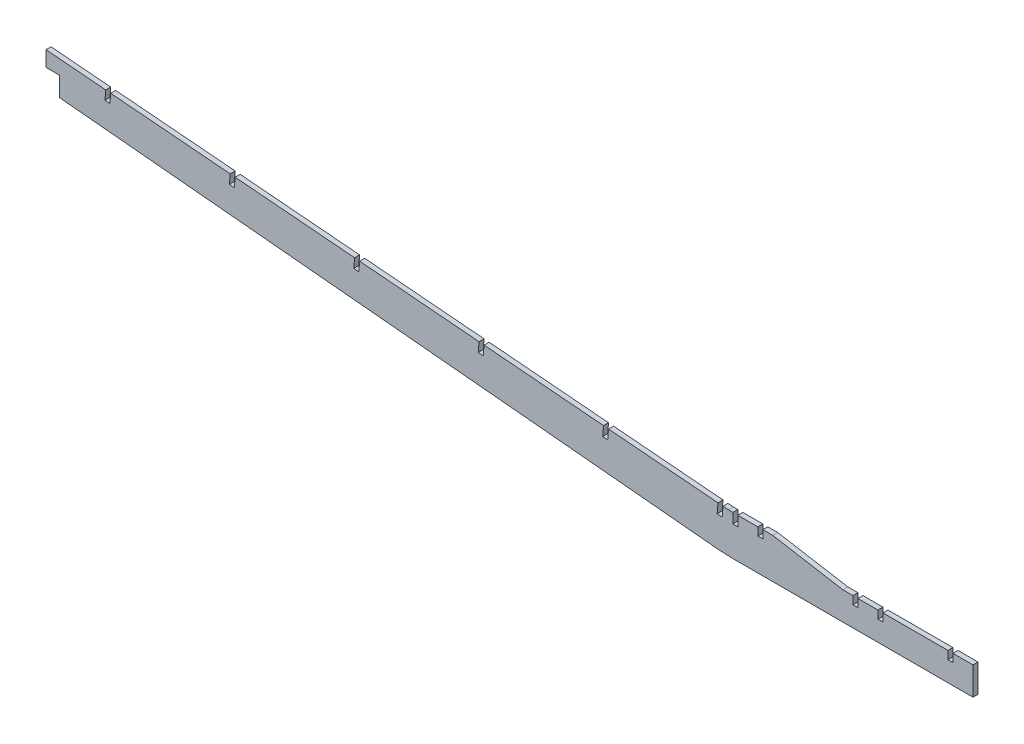
SolidWorks part; units mm, degrees
ref_plane "Front Plane" through (0, 0, 0) normal (0, 0, 1) x (1, 0, 0)
ref_plane "Top Plane" through (0, 0, 0) normal (0, 1, 0) x (1, 0, 0)
ref_plane "Right Plane" through (0, 0, 0) normal (1, 0, 0) x (0, 0, -1)
sketch "Sketch1" plane through (0, 0, 0) normal (0, 0, 1) x (1, 0, 0)
  line L0 (-951.0618, 63.2916) -> (-11.5367, -24.9026)
  line L8 (-8.3728, -25.1683) -> (-6.7788, -6.1851) construction
  line L9 (-6.7788, -6.1851) -> (-9.9426, -5.9194)
  line L10 (-9.9426, -5.9194) -> (-11.5367, -24.9026) construction
  line L11 (-11.5367, -24.9026) -> (-8.3728, -25.1683)
  line L12 (3.175, -25.5459) -> (3.175, -6.4959) construction
  line L13 (3.175, -6.4959) -> (0, -6.4959)
  line L14 (0, -6.4959) -> (0, -25.5459) construction
  line L15 (0, -25.5459) -> (3.175, -25.5459)
  line L17 (-943.9754, 109.7383) -> (-947.3666, 69.3536)
  line L19 (-8.3728, -25.1683) -> (0, -25.5459)
  line L20 (3.175, -25.5459) -> (152.4, -25.5459)
  line L21 (25.4, -0.1459) -> (69.85, -7.7659)
  line L22 (25.4, -0.1459) -> (-2.8123, -0.1459)
  line L23 (-2.8123, -0.1459) -> (-946.5481, 79.1019)
  line L24 (0, -6.4959) -> (0, -0.1459)
  line L25 (3.175, -6.4959) -> (3.175, -0.1459)
  line L26 (-6.7788, -6.1851) -> (-6.2474, 0.1426)
  line L27 (-9.9426, -5.9194) -> (-9.4113, 0.4083)
  line L28 (-9.9426, -5.9194) -> (-946.998, 73.7432)
  line L29 (69.85, -7.7659) -> (152.4, -7.7659)
  line L30 (152.4, -7.7659) -> (152.4, -25.5459)
  line L31 (76.2, -7.7659) -> (76.2, -25.5459)
  line L32 (79.375, -7.7659) -> (79.375, -25.5459)
  line L33 (76.2, -12.8459) -> (79.375, -12.8459)
  line L34 (15.875, -0.1459) -> (15.875, -5.2259)
  line L35 (15.875, -5.2259) -> (19.05, -5.2259)
  line L36 (19.05, -5.2259) -> (19.05, -0.1459)
  line L37 (92.075, -7.7659) -> (92.075, -12.8459)
  line L38 (92.075, -12.8459) -> (95.25, -12.8459)
  line L39 (95.25, -12.8459) -> (95.25, -7.7659)
  line L40 (136.525, -7.7659) -> (136.525, -12.8459)
  line L41 (136.525, -12.8459) -> (139.7, -12.8459)
  line L42 (139.7, -12.8459) -> (139.7, -7.7659)
  line L44 (-951.0618, 63.2916) -> (-950.5305, 69.6193)
  line L45 (-950.5305, 69.6193) -> (-947.3666, 69.3536)
  dimension "D1" = 25.4
  dimension "D2" = 6.35
extrude "Boss-Extrude1" add sketch "Sketch1" along normal blind 3.175
sketch "Sketch2" plane through (0, 0, 3.175) normal (0, 0, 1) x (1, 0, 0)
  line L1 (-73.9963, 64.5177) -> (-80.9723, -18.558)
  line L3 (-77.1601, 64.7834) -> (-84.1362, -18.2923)
  line L5 (-153.17, 68.7234) -> (-159.8855, -11.2491)
  line L7 (-232.3428, 72.9404) -> (-238.7996, -3.951)
  line L9 (-311.5203, 77.1018) -> (-317.7101, 3.3887)
  line L11 (-390.6978, 81.2631) -> (-396.6209, 10.7264)
  line L13 (-469.8812, 85.3537) -> (-475.5272, 18.1169)
  line L15 (-549.0652, 89.4374) -> (-554.4332, 25.5108)
  line L17 (-628.256, 93.4393) -> (-633.334, 32.9679)
  line L19 (-707.4489, 97.4177) -> (-712.2332, 40.4425)
  line L21 (-786.6506, 101.2897) -> (-791.1254, 48.0007)
  line L23 (-865.8569, 105.1088) -> (-870.014, 55.603)
  line L25 (-235.5067, 73.2061) -> (-241.9634, -3.6853)
  line L27 (-314.6841, 77.3675) -> (-320.874, 3.6544)
  line L29 (-393.8616, 81.5287) -> (-399.7848, 10.992)
  line L31 (-473.045, 85.6194) -> (-478.6911, 18.3826)
  line L33 (-552.229, 89.7031) -> (-557.5971, 25.7765)
  line L35 (-631.4199, 93.705) -> (-636.4978, 33.2336)
  line L37 (-710.6127, 97.6833) -> (-715.3971, 40.7082)
  line L39 (-789.8145, 101.5554) -> (-794.2893, 48.2664)
  line L41 (-9.9426, -5.9194) -> (-946.998, 73.7432)
  line L43 (-9.4113, 0.4083) -> (-946.5481, 79.1019)
  line L45 (-156.3339, 68.9891) -> (-163.0494, -10.9834)
  line L47 (-869.0207, 105.3745) -> (-873.1778, 55.8686)
  line M13 (-9.4113, 0.4083) -> (-946.5481, 79.1019)
extrude "Cut-Extrude1" cut sketch "Sketch2" against normal through all contours L47 L41 L23 M13 | L41 L21 L39 M13 | L41 L19 L37 M13 | L41 L17 L35 M13 | L41 L15 L33 M13 | L41 L13 L31 M13 | L41 L11 L29 M13 | L41 L9 L27 M13 | L41 L7 L25 M13 | L45 L41 L5 M13 | L41 L1 L3 M13
sketch "Sketch3" plane through (0, 0, 3.175) normal (0, 0, 1) x (1, 0, 0)
  line L0 (-435.837, 36.2162) -> (-435.837, 26.4516)
  line L1 (-397.9339, 33.0334) -> (-473.7401, 39.3991) construction
  line L2 (-435.837, 26.4516) -> (-427.1156, 26.4516)
  line L3 (-427.1156, 26.4516) -> (-427.1156, 14.1082)
  line L4 (-951.0618, 63.2916) -> (-11.5367, -24.9026) construction
  line L5 (-435.837, 36.2162) -> (-981.2137, 132.2658)
  line L6 (-981.2137, 132.2658) -> (-989.3168, 0)
  line L7 (-989.3168, 0) -> (-427.1156, 14.1082)
extrude "Cut-Extrude2" cut sketch "Sketch3" against normal blind 7.62
